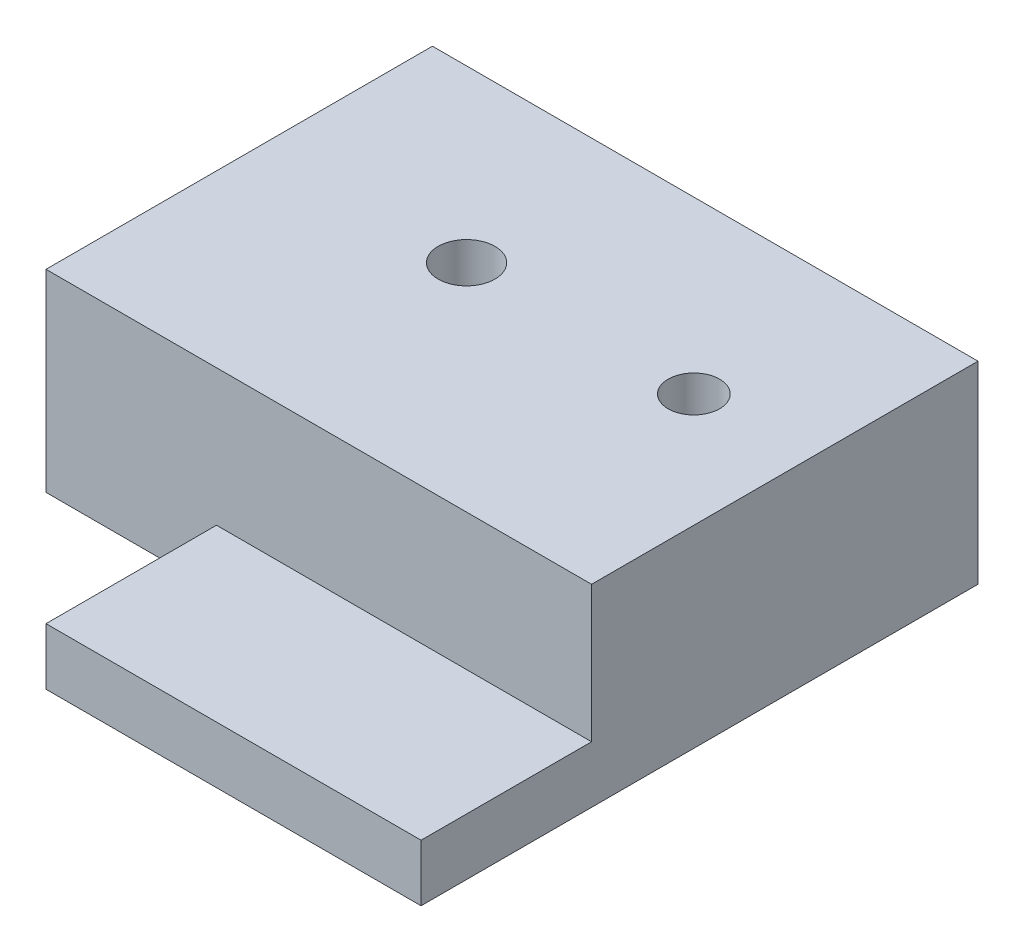
SolidWorks part; units mm, degrees
ref_plane "Front Plane" through (0, 0, 0) normal (0, 0, 1) x (1, 0, 0)
ref_plane "Top Plane" through (0, 0, 0) normal (0, 1, 0) x (1, 0, 0)
ref_plane "Right Plane" through (0, 0, 0) normal (1, 0, 0) x (0, 0, -1)
sketch "Sketch1" plane through (0, 0, 0) normal (0, 1, 0) x (1, 0, 0)
  line L1 (0, 0) -> (48, 0)
  line L2 (0, 0) -> (0, 49)
  line L3 (0, 49) -> (48, 49)
  line L4 (48, 0) -> (48, 49)
  line L5 (0, 0) -> (15, 0)
  line L6 (0, 0) -> (0, 15)
  line L7 (0, 15) -> (15, 15)
  line L8 (15, 0) -> (15, 15)
  circle A0 centre (38, 34) radius 2
  circle A1 centre (18, 34) radius 2.5
  dimension "D7" = 4
  dimension "D8" = 5
  dimension "D1" = 49
  dimension "D2" = 48
  dimension "D3" = 15
  dimension "D4" = 15
  dimension "D5" = 15
  dimension "D6" = 10
  dimension "D9" = 20
extrude "Boss-Extrude1" add sketch "Sketch1" along normal blind 5 contours L8 L1 L4 L3 L2 L7 A1 A0
sketch "Sketch2" plane through (0, 5, 0) normal (0, 1, 0) x (1, 0, 0)
  line L0 (48, 0) -> (48, 49) construction
  line L1 (0, 49) -> (48, 49)
  line L2 (0, 49) -> (0, 15)
  line L3 (0, 15) -> (48, 15)
  line L4 (48, 49) -> (48, 15)
  circle A0 centre (18, 34) radius 2.5
  circle A1 centre (38, 34) radius 2.2647
extrude "Boss-Extrude2" add sketch "Sketch2" along normal blind 12
